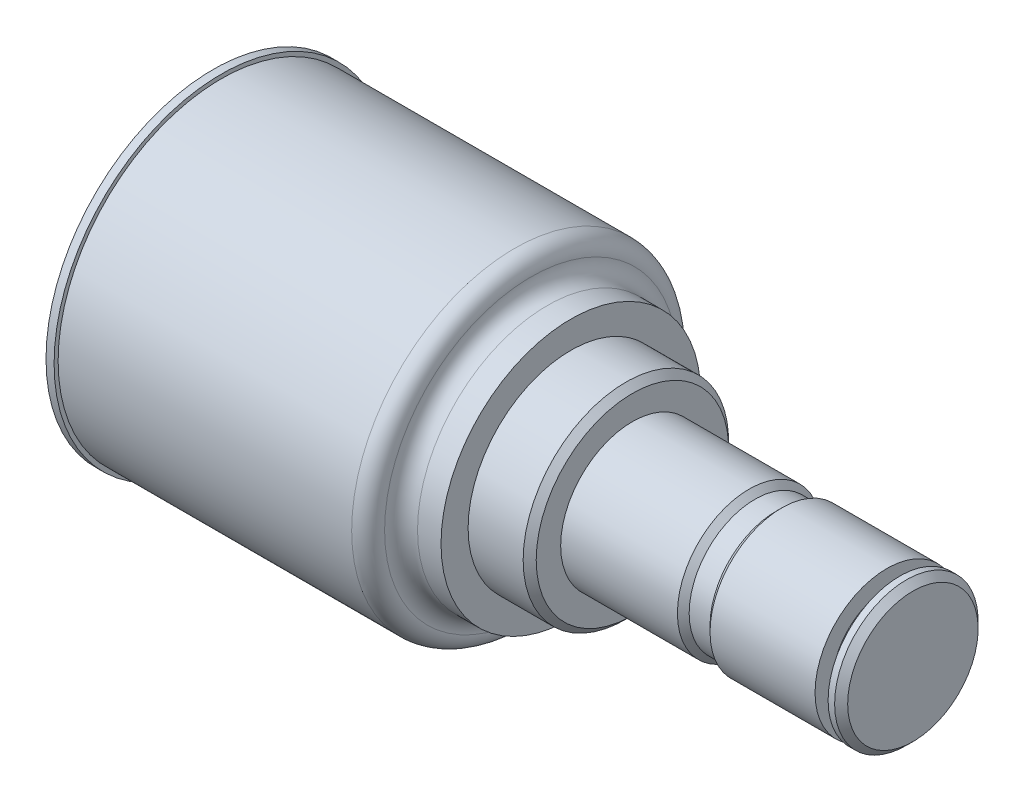
SolidWorks part; units mm, degrees
material "Plain Carbon Steel"
ref_plane "Front Plane" through (0, 0, 0) normal (0, 0, 1) x (1, 0, 0)
ref_plane "Top Plane" through (0, 0, 0) normal (0, 1, 0) x (1, 0, 0)
ref_plane "Right Plane" through (0, 0, 0) normal (1, 0, 0) x (0, 0, -1)
sketch "Sketch1" plane through (0, 0, 0) normal (0, 0, 1) x (1, 0, 0)
  line L0 (0, 0) -> (0, 32.5374)
  line L1 (0, 32.5374) -> (1.5748, 32.5374)
  line L2 (1.5748, 32.5374) -> (1.5748, 31.75)
  line L3 (1.5748, 31.75) -> (58.7248, 31.75)
  line L4 (-9.3394, 0) -> (139.4356, 0) construction
  line L5 (65.0736, 25.2749) -> (69.6468, 25.2749)
  line L6 (69.6468, 25.2749) -> (69.6468, 20.0025)
  line L7 (69.6468, 20.0025) -> (81.6356, 20.0025)
  line L8 (61.8998, 28.575) -> (61.8998, 18.389) construction
  line L9 (81.6356, 20.0025) -> (81.6356, 13.97)
  line L10 (81.6356, 13.97) -> (104.3686, 13.97)
  line L11 (136.2456, 13.97) -> (136.2456, 0)
  line L12 (136.2456, 0) -> (0, 0)
  line L13 (104.3686, 13.97) -> (105.5116, 12.827)
  line L14 (105.5116, 12.827) -> (109.5756, 12.827)
  line L15 (109.5756, 12.827) -> (110.7186, 13.97)
  line L16 (110.7186, 13.97) -> (131.1656, 13.97)
  line L17 (131.1656, 13.97) -> (131.1656, 10.5918)
  line L18 (131.1656, 10.5918) -> (133.7056, 10.5918)
  line L19 (133.7056, 10.5918) -> (133.7056, 13.97)
  line L20 (133.7056, 13.97) -> (136.2456, 13.97)
  arc A0 (61.8992, 28.5124) -> (58.7248, 31.75) centre (58.7248, 28.575) ccw
  arc A1 (61.8992, 28.5124) -> (65.0736, 25.2749) centre (65.0736, 28.4499) ccw
  dimension "D4" = 3.175
  dimension "D1" = 65.0748
  dimension "D2" = 63.5
  dimension "D3" = 1.5748
  dimension "D5" = 57.15
  dimension "D6" = 71.172
  dimension "D7" = 40.005
  dimension "D8" = 77.5208
  dimension "D9" = 27.94
  dimension "D10" = 66.5988
  dimension "D11" = 54.61
  dimension "D12" = 25.527
  dimension "D13" = 31.877
  dimension "D14" = 25.654
  dimension "D15" = 45
  dimension "D16" = 2.54
  dimension "D17" = 5.08
  dimension "D18" = 21.1836
revolve "Revolve1" add sketch "Sketch1"
chamfer "Chamfer1" distance 1.27 angle 45 2 edges at (81.6356, 0, 20.0025) (136.2456, 0, 13.97)
sketch "Sketch2" plane through (0, 0, 0) normal (-1, 0, 0) x (0, 0, 1)
  point P0 (0, 0)
